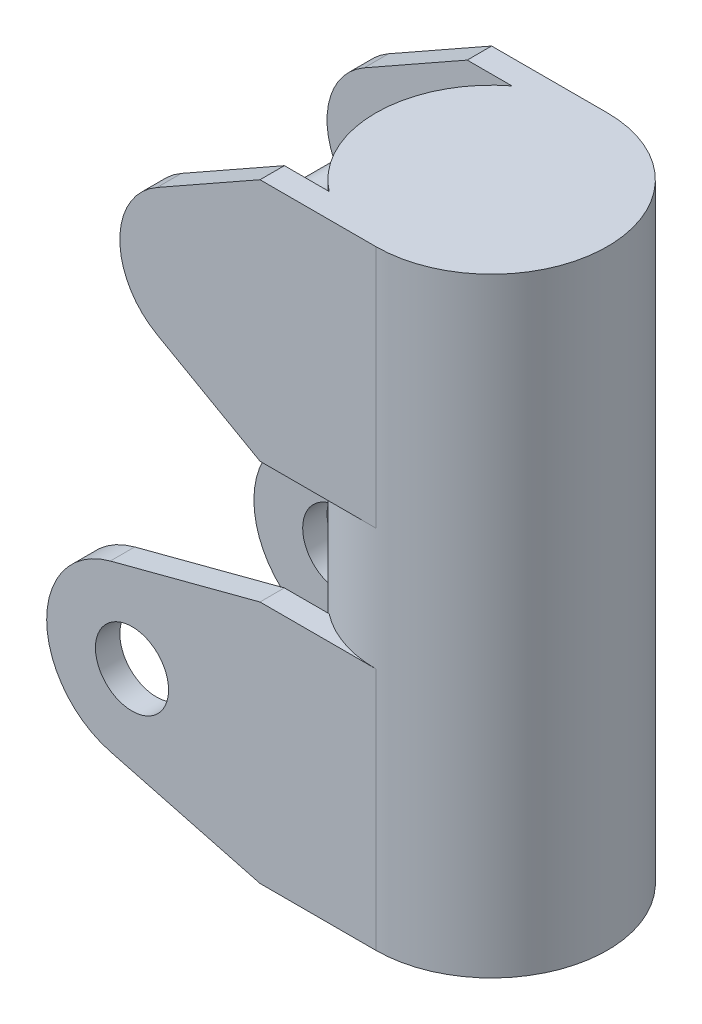
SolidWorks part; units mm, degrees
material "AISI 4340 Steel, normalized"
ref_plane "Front Plane" through (0, 0, 0) normal (0, 0, 1) x (1, 0, 0)
ref_plane "Top Plane" through (0, 0, 0) normal (0, 1, 0) x (1, 0, 0)
ref_plane "Right Plane" through (0, 0, 0) normal (1, 0, 0) x (0, 0, -1)
sketch "Sketch1" plane through (0, 0, 0) normal (0, 1, 0) x (1, 0, 0)
  circle A0 centre (0, 0) radius 95
  dimension "D1" = 190
extrude "Boss-Extrude1" add sketch "Sketch1" along normal blind 500
shell "Shell1" thickness 10
ref_plane "Plane1" through (0, 0, -95) normal (0, 0, -1) x (-1, 0, 0)
sketch "Sketch2" plane through (0, 0, -95) normal (0, 0, -1) x (-1, 0, 0)
  line L0 (0, 0) -> (95, 0)
  line L1 (-95, 0) -> (95, 0) construction
  line L2 (95, 0) -> (217.8069, 32.3028)
  line L3 (217.8069, 167.6972) -> (95, 200)
  line L4 (95, 0) -> (95, 500) construction
  line L5 (95, 200) -> (0, 200)
  line L6 (0, 200) -> (0, 0)
  line L7 (0, 500) -> (95, 500)
  line L8 (95, 500) -> (-95, 500) construction
  line L9 (95, 500) -> (179.5197, 452.2359)
  line L10 (179.5197, 347.7641) -> (95, 300)
  line L11 (95, 300) -> (0, 300)
  line L12 (0, 300) -> (0, 500)
  arc A0 (217.8069, 32.3028) -> (217.8069, 167.6972) centre (200, 100) ccw
  circle A1 centre (200, 100) radius 30
  arc A2 (179.5197, 347.7641) -> (179.5197, 452.2359) centre (150, 400) ccw
  circle A3 centre (150, 400) radius 20 construction
  point P15 (0, 100)
  point P27 (0, 400)
  dimension "D1" = 60
  dimension "D2" = 40
  dimension "D5" = 40
  dimension "D6" = 40
  dimension "D3" = 200
  dimension "D4" = 200
  dimension "D7" = 200
  dimension "D8" = 150
extrude "Boss-Extrude2" add sketch "Sketch2" against normal blind 20
sketch "Sketch3" plane through (0, 500, 0) normal (0, 1, 0) x (1, 0, 0)
  line L0 (-95, 0) -> (95, 0) construction
  arc A0 (-58.3095, 75) -> (0, 95) centre (0, 0) ccw construction
ref_plane "Plane2" through (0, 0, 0) normal (0, 0, -1) x (-1, 0, 0)
mirror "Mirror1" about plane through (0, 0, 0) normal (0, 0, -1) of "Boss-Extrude2"
sketch "Sketch4" plane through (0, 0, 0) normal (0, 0, 1) x (1, 0, 0)
  circle A0 centre (-150, 400) radius 20 construction
  circle A1 centre (-150, 400) radius 20
extrude "Boss-Extrude3" add sketch "Sketch4" along normal mid plane 190
